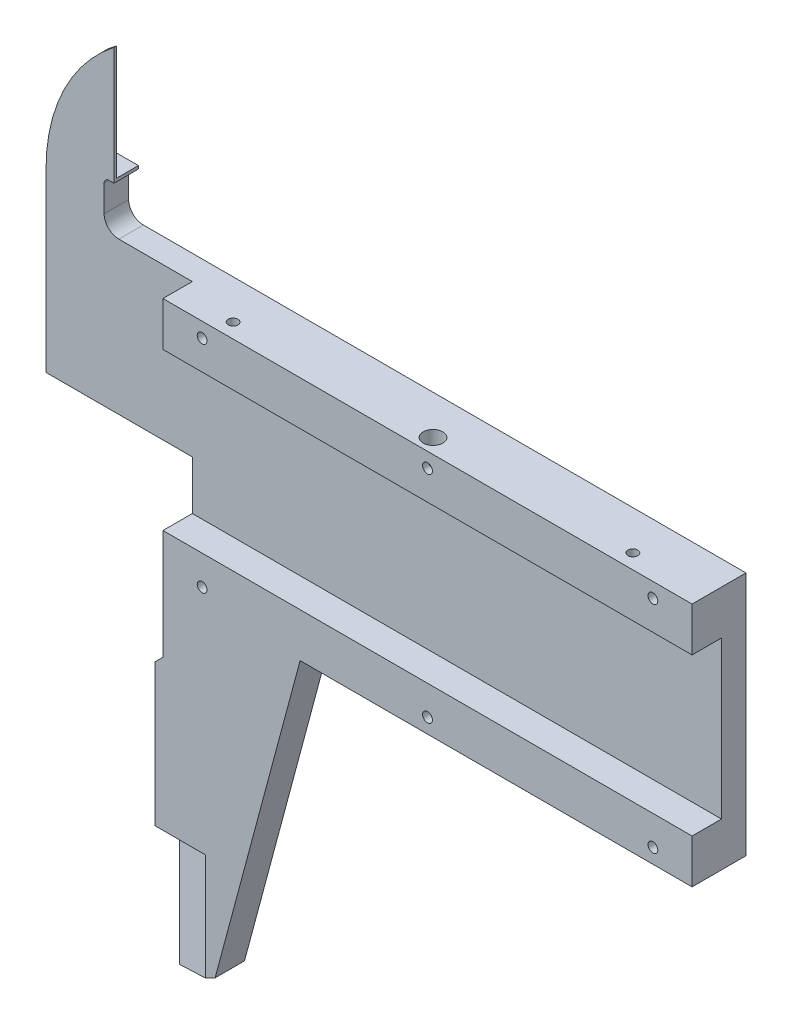
SolidWorks part; units mm, degrees
material "1.4000 (X6Cr13)"
ref_plane "Front Plane" through (0, 0, 0) normal (0, 0, 1) x (1, 0, 0)
ref_plane "Top Plane" through (0, 0, 0) normal (0, 1, 0) x (1, 0, 0)
ref_plane "Right Plane" through (0, 0, 0) normal (1, 0, 0) x (0, 0, -1)
sketch "Sketch1" plane through (0, 0, 0) normal (0, 0, 1) x (1, 0, 0)
  line L0 (0, 0) -> (-70.8407, 0) construction
  line L1 (0, 0) -> (0, 12.5)
  line L2 (0, 12.5) -> (-61.5, 12.5)
  line L3 (-63, 14) -> (-63, 16.6935)
  line L4 (-62.5, 17.1935) -> (-62, 17.1935)
  line L5 (-62, 17.1935) -> (-62, 29.1935)
  line L6 (0, 0) -> (0, -12.5)
  line L7 (0, -12.5) -> (-40, -12.5)
  line L8 (-40, -12.5) -> (-48.6761, -44.8797)
  line L9 (-48.6761, -44.8797) -> (-54.8, -48)
  line L10 (-54.8, -48) -> (-54.8, -20)
  line L11 (-54.8, -20) -> (-54, -19.2)
  line L12 (-54, -19.2) -> (-54, -3)
  line L13 (-54, -3) -> (-68.93, -3)
  line L14 (-68.93, -3) -> (-68.93, 15)
  arc A0 (-68.93, 15) -> (-62, 29.1935) centre (-50.93, 15) cw
  arc A1 (-61.5, 12.5) -> (-63, 14) centre (-61.5, 14) cw
  arc A2 (-63, 16.6935) -> (-62.5, 17.1935) centre (-62.5, 16.6935) cw
  point P27 (-63, 17.1935)
  dimension "D11" = 18
  dimension "D17" = 1.5
  dimension "D18" = 0.5
  dimension "D1" = 54
  dimension "D2" = 25
  dimension "D3" = 35.5
  dimension "D4" = 63
  dimension "D5" = 105
  dimension "D6" = 28
  dimension "D7" = 135
  dimension "D8" = 0.8
  dimension "D9" = 45
  dimension "D10" = 18
  dimension "D12" = 12
  dimension "D13" = 1
  dimension "D14" = 5.93
  dimension "D15" = 68.93
  dimension "D16" = 14
  dimension "D19" = 6.93
extrude "Boss-Extrude1" add sketch "Sketch1" along normal mid plane 5.5
sketch "Sketch2" plane through (0, 0, 2.75) normal (0, 0, 1) x (1, 0, 0)
  line L0 (0, -12.5) -> (0, 12.5) construction
  line L1 (0, -8) -> (-54, -8)
  line L2 (0, -8) -> (0, 8)
  line L3 (0, 8) -> (-54, 8)
  line L6 (-54, -8) -> (-84.5569, -8)
  line L7 (-54, 8) -> (-54, 35.3716)
  line L8 (-54, 35.3716) -> (-84.5569, 35.3716)
  line L9 (-84.5569, -8) -> (-84.5569, 35.3716)
  dimension "D1" = 16
  dimension "D2" = 54
  dimension "D3" = 54
extrude "Cut-Extrude1" cut sketch "Sketch2" against normal blind 3
sketch "Sketch3" plane through (0, 0, 2.75) normal (0, 0, 1) x (1, 0, 0)
  line L0 (0, 0) -> (-86.3442, 0) construction
  line L1 (-54, 8) -> (-54, 12.5) construction
  line L2 (0, 12.5) -> (-54, 12.5) construction
  line L3 (0, 8) -> (0, 12.5) construction
  circle A0 centre (-4, 11) radius 0.5
  circle A1 centre (-27, 11) radius 0.5
  circle A2 centre (-50, 11) radius 0.5
  circle A3 centre (-50, -11) radius 0.5
  circle A4 centre (-27, -11) radius 0.5
  circle A5 centre (-4, -11) radius 0.5
  dimension "D1" = 27
  dimension "D2" = 4
  dimension "D3" = 1.5
  dimension "D4" = 4
  dimension "D5" = 1
extrude "Cut-Extrude2" cut sketch "Sketch3" against normal blind 1.25
sketch "Sketch4" plane through (0, 12.5, 0) normal (0, 1, 0) x (1, 0, 0)
  line L0 (-68.93, 2.75) -> (-62, 0.5)
  line L1 (-62, 0.25) -> (-62, 2.75) construction
  line L2 (-62, 0.5) -> (-62, 2.75)
  line L3 (-62, 2.75) -> (-68.93, 2.75)
  dimension "D1" = 0.25
extrude "Cut-Extrude3" cut sketch "Sketch4" against normal blind 12.5 from offset 17.5
sketch "Sketch5" plane through (0, -12.5, 0) normal (0, -1, 0) x (1, 0, 0)
  line L0 (-54.8, 2.75) -> (-54.8, -2.75) construction
  line L1 (-54.8, -0.25) -> (-40, -0.25)
  line L2 (-54.8, -0.25) -> (-54.8, -2.75)
  line L3 (-54.8, -2.75) -> (-40, -2.75)
  line L4 (-40, -0.25) -> (-40, -2.75)
  line L5 (-68.93, -0.25) -> (-54, -0.25) construction
extrude "Cut-Extrude4" cut sketch "Sketch5" along normal through all
sketch "Sketch6" plane through (0, -12.5, 0) normal (0, -1, 0) x (1, 0, 0)
  line L0 (-54.8, 2.75) -> (-54.8, 0.25)
  line L1 (-54.8, 2.75) -> (-54.8, -0.25) construction
  line L2 (-54.8, 0.25) -> (-49.6742, 2.75)
  line L3 (-54.8, 2.75) -> (-48.6761, 2.75) construction
  line L4 (-49.6742, 2.75) -> (-54.8, 2.75)
  line L5 (-68.93, -0.25) -> (-54, -0.25) construction
  line L6 (-40, -0.25) -> (-54, -0.25) construction
  dimension "D1" = 0.5
  dimension "D2" = 26
extrude "Cut-Extrude5" cut sketch "Sketch6" against normal blind 13.5 from offset 35.5
sketch "Sketch7" plane through (0, 12.5, 0) normal (0, 1, 0) x (1, 0, 0)
  line L0 (0, -2.75) -> (0, 2.75) construction
  line L2 (0, -2.75) -> (-54, -2.75) construction
  circle A0 centre (-7.54, -1.25) radius 0.5
  circle A1 centre (-48.34, -1.25) radius 0.5
  dimension "D1" = 1
  dimension "D2" = 7.54
  dimension "D3" = 40.8
  dimension "D4" = 1.5
extrude "Cut-Extrude6" cut sketch "Sketch7" against normal blind 3
sketch "Sketch8" plane through (0, 12.5, 0) normal (0, 1, 0) x (1, 0, 0)
  line L0 (0, -2.75) -> (-54, -2.75) construction
  circle A0 centre (-27.94, -1.25) radius 1
  circle A1 centre (-7.54, -1.25) radius 0.5 construction
  dimension "D1" = 2
  dimension "D2" = 20.4
  dimension "D3" = 1.5
extrude "Cut-Extrude7" cut sketch "Sketch8" against normal up to next
